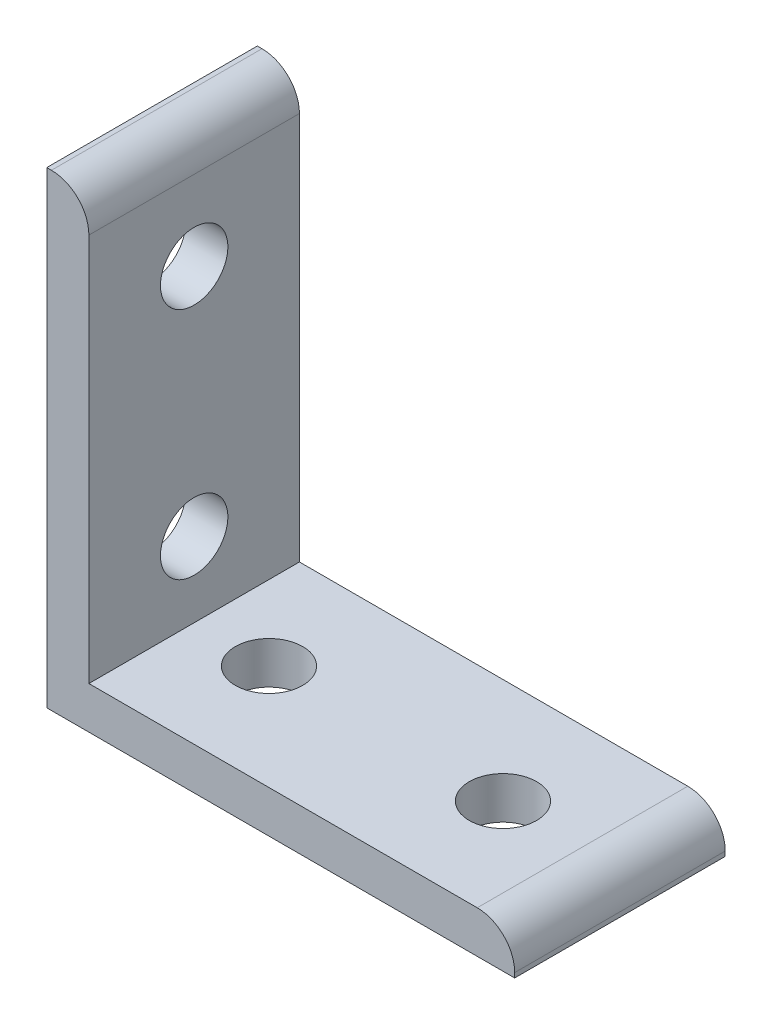
SolidWorks part; units mm, degrees
ref_plane "Front Plane" through (0, 0, 0) normal (0, 0, 1) x (1, 0, 0)
ref_plane "Top Plane" through (0, 0, 0) normal (0, 1, 0) x (1, 0, 0)
ref_plane "Right Plane" through (0, 0, 0) normal (1, 0, 0) x (0, 0, -1)
sketch "Sketch1" plane through (0, 0, 0) normal (0, 0, 1) x (1, 0, 0)
  line L0 (0, 50) -> (0, 0)
  line L1 (0, 0) -> (50, 0)
  line L2 (4.5, 50) -> (4.5, 4.5)
  line L3 (4.5, 4.5) -> (50, 4.5)
  line L4 (0, 50) -> (4.5, 50)
  line L5 (50, 4.5) -> (50, 0)
  dimension "D1" = 50
  dimension "D2" = 4.5
extrude "Boss-Extrude1" add sketch "Sketch1" along normal blind 22.5
sketch "Sketch2" plane through (0, 0, 0) normal (-1, 0, 0) x (0, 0, 1)
  line L0 (22.5, 0) -> (0, 0) construction
  circle A0 centre (11.25, 37.5) radius 3.6
  circle A1 centre (11.25, 12.5) radius 3.6
  point P4 (0, 0)
  point P7 (11.25, 0)
  dimension "D1" = 7.2
  dimension "D2" = 12.5
  dimension "D3" = 25
extrude "Cut-Extrude1" cut sketch "Sketch2" against normal through all
sketch "Sketch3" plane through (0, 0, 0) normal (0, -1, 0) x (1, 0, 0)
  line L0 (0, 22.5) -> (0, 0) construction
  circle A0 centre (37.5, 11.25) radius 3.6
  circle A1 centre (12.5, 11.25) radius 3.6
  point P4 (0, 0)
  point P7 (0, 11.25)
  point P8 (33.412, 11.25)
  dimension "D2" = 7.2
  dimension "D1" = 25
  dimension "D3" = 12.5
extrude "Cut-Extrude2" cut sketch "Sketch3" against normal through all
fillet "Fillet1" radius 4 2 edges at (50, 4.5, 11.25) (4.5, 50, 11.25)
